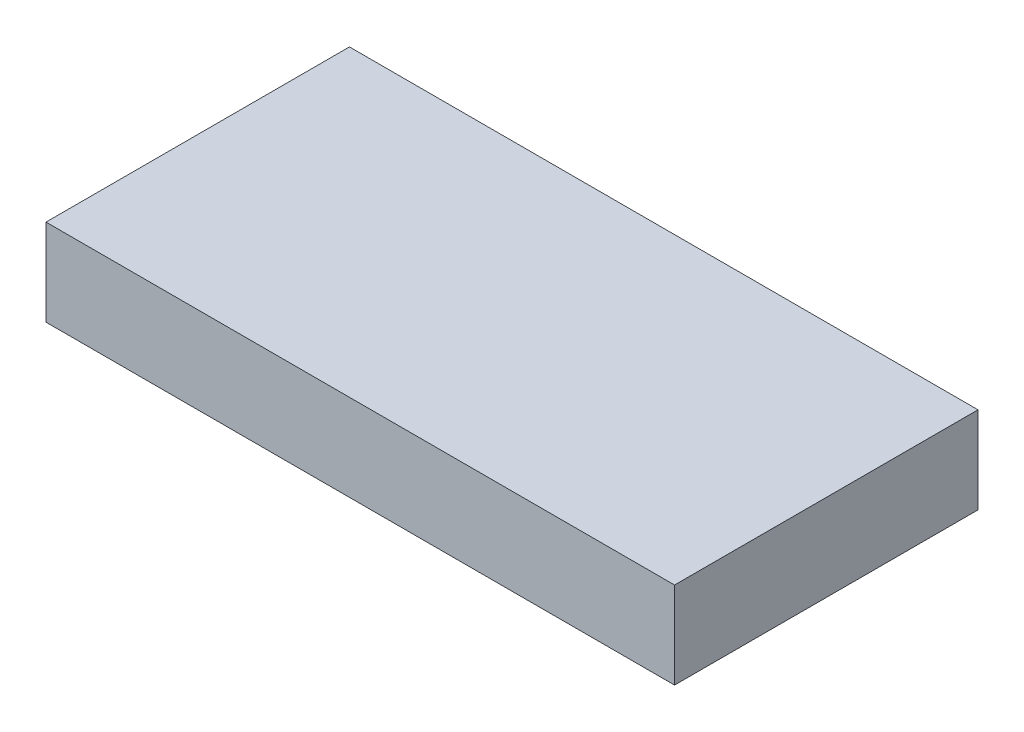
SolidWorks part; units mm, degrees
ref_plane "Front Plane" through (0, 0, 0) normal (0, 0, 1) x (1, 0, 0)
ref_plane "Top Plane" through (0, 0, 0) normal (0, 1, 0) x (1, 0, 0)
ref_plane "Right Plane" through (0, 0, 0) normal (1, 0, 0) x (0, 0, -1)
other "Bounding Box"
ref_plane "Default Plane" through (-8.9266, -12.7485, 0) normal (-0.1736, 0.9848, 0) x (0.9848, 0.1736, 0)
sketch "Sketch1" plane through (0, 0, 0) normal (0, 1, 0) x (1, 0, 0)
  line L1 (-14.5, -7) -> (14.5, -7)
  line L2 (-14.5, -7) -> (-14.5, 7)
  line L3 (-14.5, 7) -> (14.5, 7)
  line L4 (14.5, -7) -> (14.5, 7)
  line L5 (-14.5, -7) -> (14.5, 7) construction
  line L6 (-14.5, 7) -> (14.5, -7) construction
  point P0 (0, 0)
  dimension "D1" = 29
  dimension "D2" = 14
extrude "Boss-Extrude1" add sketch "Sketch1" along normal mid plane 4
